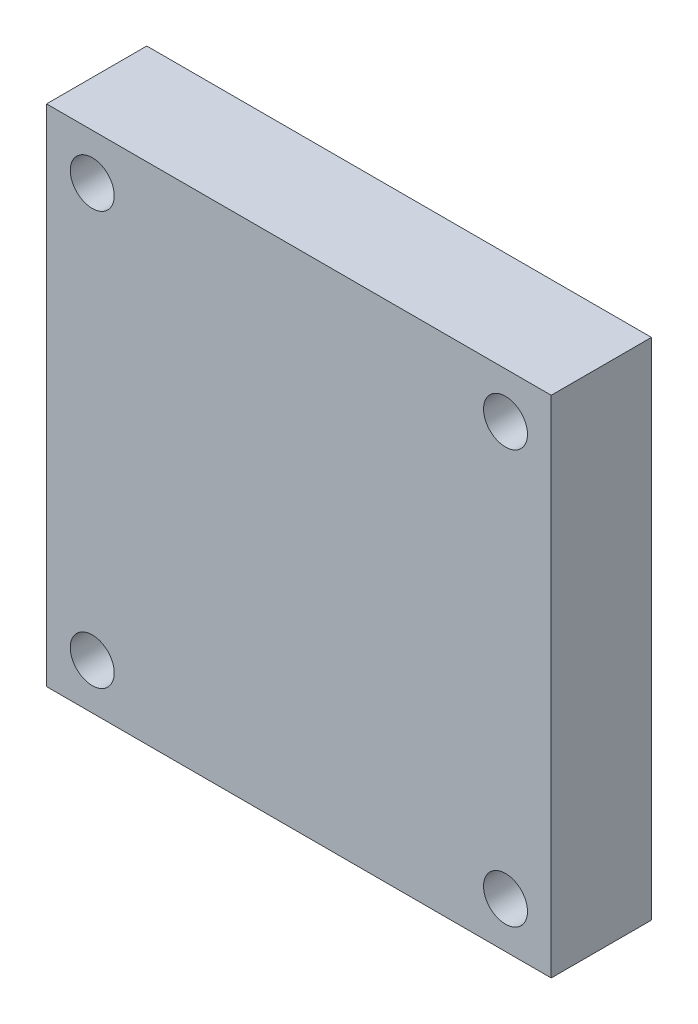
SolidWorks part; units mm, degrees
ref_plane "Ebene vorne" through (0, 0, 0) normal (0, 0, 1) x (1, 0, 0)
ref_plane "Ebene oben" through (0, 0, 0) normal (0, 1, 0) x (1, 0, 0)
ref_plane "Ebene rechts" through (0, 0, 0) normal (1, 0, 0) x (0, 0, -1)
sketch "Skizze1" plane through (0, 0, 0) normal (0, 0, 1) x (1, 0, 0)
  line L0 (0, 0) -> (28.7, 0)
  line L1 (28.7, 0) -> (28.7, 28.7)
  line L2 (28.7, 28.7) -> (-28.7, 28.7)
  line L3 (-28.7, 28.7) -> (-28.7, -28.7)
  line L4 (-28.7, -28.7) -> (28.7, -28.7)
  line L5 (28.7, -28.7) -> (28.7, 0)
  dimension "D1" = 57.4
  dimension "D2" = 57.4
  dimension "D3" = 28.7
  dimension "D4" = 28.7
extrude "Aufsatz-Linear austragen1" add sketch "Skizze1" along normal blind 11.4
sketch "Skizze2" plane through (0, 0, 11.4) normal (0, 0, 1) x (1, 0, 0)
  line L1 (-23.5, 23.5) -> (23.5, 23.5)
  line L2 (-23.5, 23.5) -> (-23.5, -23.5)
  line L3 (-23.5, -23.5) -> (23.5, -23.5)
  line L4 (23.5, 23.5) -> (23.5, -23.5)
  line L5 (-28.7, 28.7) -> (-28.7, -28.7) construction
  line L6 (28.7, 28.7) -> (-28.7, 28.7) construction
  dimension "D1" = 47
  dimension "D2" = 47
  dimension "D3" = 5.2
  dimension "D4" = 5.2
hole_wizard "Ø5.0 (5) Durchmesser Bohrung1" positions "Skizze4" profile "Skizze3" hole size "Ø5.0" standard "ANSI Metrisch" end condition through all
sketch "Skizze4" plane through (0, 0, 11.4) normal (0, 0, 1) x (1, 0, 0)
  point P0 (-23.5, 23.5)
  point P3 (23.5, 23.5)
  point P6 (23.5, -23.5)
  point P9 (-23.5, -23.5)
sketch "Skizze3" plane through (-23.5, 23.5, 11.4) normal (1, 0, 0) x (0, -1, 0)
  line L0 (0, 0) -> (0, 11.4)
  line L1 (0, 11.4) -> (2.5, 11.4)
  line L2 (2.5, 11.4) -> (2.5, 0)
  line L5 (2.5, 0) -> (0, 0)
  line L11 (0, -6.35) -> (0, 107.95) construction
  dimension "Bohrerdurchmesser" = 5
  dimension "Bohrungstiefe" = 11.4
